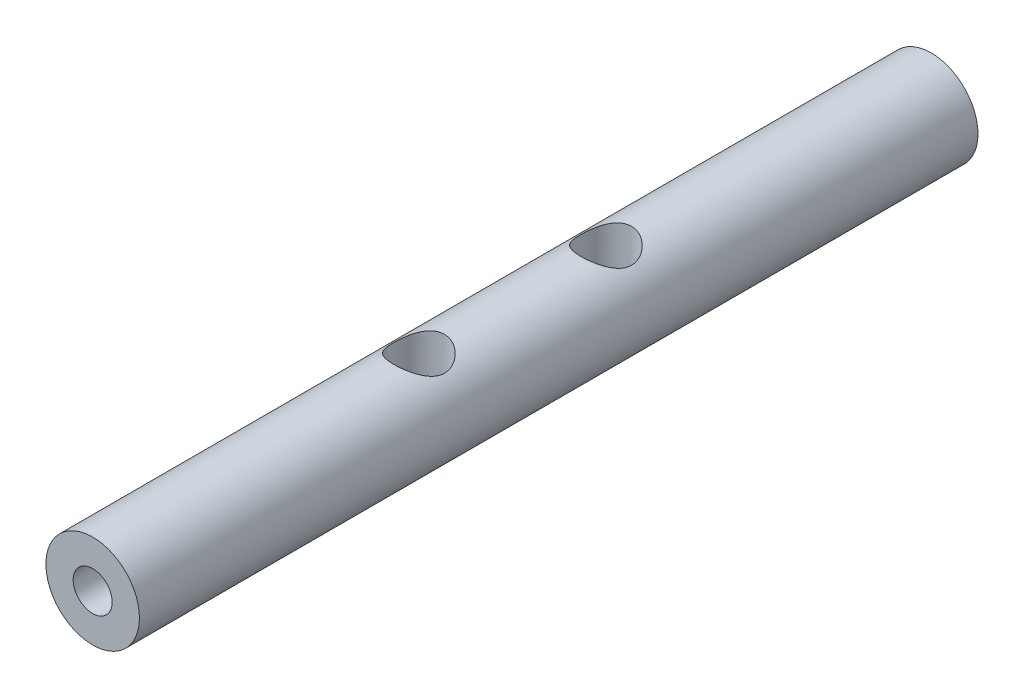
SolidWorks part; units mm, degrees
material "炭素鋼(鋳造)"
ref_plane "正面" through (0, 0, 0) normal (0, 0, 1) x (1, 0, 0)
ref_plane "平面" through (0, 0, 0) normal (0, 1, 0) x (1, 0, 0)
ref_plane "右側面" through (0, 0, 0) normal (1, 0, 0) x (0, 0, -1)
sketch "ｽｹｯﾁ1" plane through (0, 0, 0) normal (0, 0, 1) x (1, 0, 0)
  circle A0 centre (0, 0) radius 3
  dimension "D1" = 6
extrude "ﾎﾞｽ - 押し出し1" add sketch "ｽｹｯﾁ1" along normal blind 53.8
sketch "ｽｹｯﾁ2" plane through (0, 0, 53.8) normal (0, 0, 1) x (1, 0, 0)
  circle A0 centre (0, 0) radius 3
  circle A1 centre (0, 0) radius 5.2499
  dimension "D1" = 6
sketch "ｽｹｯﾁ3" plane through (0, 0, 0) normal (0, 0, -1) x (-1, 0, 0)
  circle A0 centre (0, 0) radius 3
  circle A1 centre (0, 0) radius 5.9607
  dimension "D1" = 6
hole_wizard "M4x0.7 ねじ穴1" positions "3Dｽｹｯﾁ5" profile "ｽｹｯﾁ6" tap size "M4x0.7" standard "JIS"
sketch3d "3Dｽｹｯﾁ5"
  point P0 (0.0291, 2.9999, 32.9)
  point P2 (0.0291, 2.9999, 20.9)
  dimension "D1" = 12
  dimension "D2" = 20.9
sketch "ｽｹｯﾁ6" plane through (0.0291, 2.9999, 32.9) normal (0, 0, 1) x (-1, 0.0097, 0)
  line L0 (0, 0) -> (0, 12.4914)
  line L1 (0, 12.4914) -> (1.65, 11.5)
  line L2 (1.65, 11.5) -> (1.65, 0)
  line L5 (1.65, 0) -> (0, 0)
  line L10 (0, 12.4914) -> (-1.65, 11.5) construction
  line L11 (0, -6.35) -> (0, 107.95) construction
  dimension "ねじ下穴ﾄﾞﾘﾙ直径" = 3.3
  dimension "ねじ下穴ﾄﾞﾘﾙの深さ" = 11.5
  dimension "ﾄﾞﾘﾙ角度" = 118
cosmetic thread "穴のねじ山1" parameters "D1"=7, "D2"=4
cosmetic thread "穴のねじ山3" parameters "D1"=7, "D2"=4
hole_wizard "M3x0.5 ねじ穴1" positions "3Dｽｹｯﾁ6" profile "ｽｹｯﾁ7" tap size "M3x0.5" standard "JIS"
sketch3d "3Dｽｹｯﾁ6"
  line L0 (0, 0, 53.8) -> (0, 0, 0) construction
  point P0 (0, 0, 0)
  point P3 (0, 0, 0)
  point P5 (0, 0, 53.8)
sketch "ｽｹｯﾁ7" plane through (0, 0, 53.8) normal (1, 0, 0) x (0, -1, 0)
  line L0 (0, 0) -> (0, 9.2511)
  line L1 (0, 9.2511) -> (1.25, 8.5)
  line L2 (1.25, 8.5) -> (1.25, 0)
  line L5 (1.25, 0) -> (0, 0)
  line L10 (0, 9.2511) -> (-1.25, 8.5) construction
  line L11 (0, -6.35) -> (0, 107.95) construction
  dimension "ねじ下穴ﾄﾞﾘﾙ直径" = 2.5
  dimension "ねじ下穴ﾄﾞﾘﾙの深さ" = 8.5
  dimension "ﾄﾞﾘﾙ角度" = 118
cosmetic thread "穴のねじ山4" parameters "D1"=6, "D2"=3
cosmetic thread "穴のねじ山5" parameters "D1"=6, "D2"=3
cosmetic thread "穴のねじ山6" parameters "D1"=6, "D2"=3
hole_wizard "M3x0.5 ねじ穴2" positions "ｽｹｯﾁ8" profile "ｽｹｯﾁ9" tap size "M3x0.5" standard "JIS"
sketch "ｽｹｯﾁ8" plane through (0, 0, 0) normal (0, 0, -1) x (-1, 0, 0)
  point P0 (0, 0)
sketch "ｽｹｯﾁ9" plane through (0, 0, 0) normal (1, 0, 0) x (0, 1, 0)
  line L0 (0, 0) -> (0, 9.2511)
  line L1 (0, 9.2511) -> (1.25, 8.5)
  line L2 (1.25, 8.5) -> (1.25, 0)
  line L5 (1.25, 0) -> (0, 0)
  line L10 (0, 9.2511) -> (-1.25, 8.5) construction
  line L11 (0, -6.35) -> (0, 107.95) construction
  dimension "ねじ下穴ﾄﾞﾘﾙ直径" = 2.5
  dimension "ねじ下穴ﾄﾞﾘﾙの深さ" = 8.5
  dimension "ﾄﾞﾘﾙ角度" = 118
cosmetic thread "穴のねじ山7" parameters "D1"=6, "D2"=3
